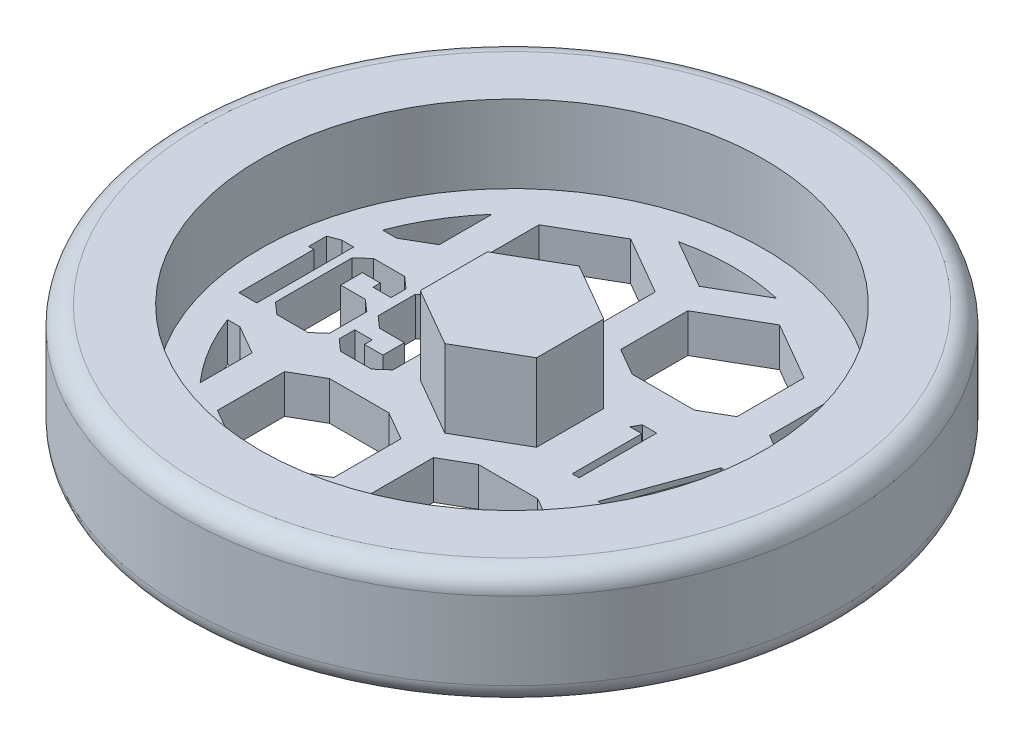
SolidWorks part; units mm, degrees
ref_plane "Front Plane" through (0, 0, 0) normal (0, 0, 1) x (1, 0, 0)
ref_plane "Top Plane" through (0, 0, 0) normal (0, 1, 0) x (1, 0, 0)
ref_plane "Right Plane" through (0, 0, 0) normal (1, 0, 0) x (0, 0, -1)
sketch "Sketch1" plane through (0, 0, 0) normal (0, 0, 1) x (1, 0, 0)
  line L0 (0, 0) -> (25.4, 0)
  line L1 (26.9875, 1.5875) -> (26.9875, 7.9375)
  line L2 (25.4, 9.525) -> (20.6375, 9.525)
  line L3 (20.6375, 9.525) -> (20.6375, 3.175)
  line L4 (20.6375, 3.175) -> (0, 3.175)
  line L5 (0, 3.175) -> (0, 0)
  arc A0 (25.4, 0) -> (26.9875, 1.5875) centre (25.4, 1.5875) ccw
  arc A1 (26.9875, 7.9375) -> (25.4, 9.525) centre (25.4, 7.9375) ccw
  dimension "D5" = 1.5875
  dimension "D1" = 3.175
  dimension "D2" = 6.35
  dimension "D3" = 20.6375
  dimension "D4" = 6.35
revolve "Revolve1" add sketch "Sketch1" angle 360 about L5
sketch "Sketch2" plane through (0, 3.175, 0) normal (0, 1, 0) x (1, 0, 0)
  line L1 (0, 5.4993) -> (-4.7625, 2.7496)
  line L2 (-4.7625, 2.7496) -> (-4.7625, -2.7496)
  line L3 (-4.7625, -2.7496) -> (0, -5.4993)
  line L4 (0, -5.4993) -> (4.7625, -2.7496)
  line L5 (4.7625, -2.7496) -> (4.7625, 2.7496)
  line L6 (4.7625, 2.7496) -> (0, 5.4993)
  circle A0 centre (0, 0) radius 4.7625 construction
  dimension "D1" = 9.525
extrude "Boss-Extrude1" add sketch "Sketch2" along normal blind 6.35
sketch "Sketch3" plane through (0, 3.175, 0) normal (0, 1, 0) x (1, 0, 0)
  line L0 (-4.7625, 0) -> (-20.6375, 0) construction
  line L1 (-4.7625, 2.7496) -> (-4.7625, -2.7496) construction
  line L2 (-4.7625, -3.9688) -> (-20.6375, -3.9688) construction
  line L3 (4.7625, 0) -> (20.6375, 0) construction
  line L4 (4.7625, -2.7496) -> (4.7625, 2.7496) construction
  line L5 (4.7625, -3.175) -> (20.6375, -3.175) construction
  circle A0 centre (0, 0) radius 20.6375 construction
  text T0 "169" font "Jersey M54" height 7.9375
  text T1 "1/4" font "Century Gothic" height 6.35
  dimension "D1" = 3.9688
  dimension "D2" = 3.175
extrude "Cut-Extrude1" cut sketch "Sketch3" against normal through all both and the other way through all
sketch "Sketch4" plane through (0, 3.175, 0) normal (0, 1, 0) x (1, 0, 0)
  line L0 (0, -6.35) -> (0, 6.35)
  line L1 (-16.9469, 6.35) -> (16.9469, 6.35)
  line L2 (-16.9469, -6.35) -> (16.9469, -6.35)
  line L3 (7.4295, -2.7496) -> (12.192, -5.4993)
  line L4 (0, -5.4993) -> (4.7625, -2.7496)
  line L5 (4.7625, -2.7496) -> (4.7625, 2.7496)
  line L6 (4.7625, 2.7496) -> (0, 5.4993)
  line L7 (0, 5.4993) -> (-4.7625, 2.7496)
  line L8 (-4.7625, 2.7496) -> (-4.7625, -2.7496)
  line L9 (-4.7625, -2.7496) -> (0, -5.4993)
  line L10 (6.0325, -15.9479) -> (10.795, -13.1982)
  line L11 (10.795, -13.1982) -> (10.795, -7.699)
  line L12 (10.795, -7.699) -> (6.0325, -4.9493)
  line L13 (6.0325, -4.9493) -> (1.27, -7.699)
  line L14 (1.27, -7.699) -> (1.27, -13.1982)
  line L15 (1.27, -13.1982) -> (6.0325, -15.9479)
  line L16 (7.4295, 2.7496) -> (7.4295, -2.7496)
  line L17 (12.192, 5.4993) -> (7.4295, 2.7496)
  line L18 (16.9545, 2.7496) -> (12.192, 5.4993)
  line L19 (16.9545, -2.7496) -> (16.9545, 2.7496)
  line L20 (12.192, -5.4993) -> (16.9545, -2.7496)
  line L21 (18.2245, -15.9479) -> (22.987, -13.1982)
  line L22 (22.987, -13.1982) -> (22.987, -7.699)
  line L23 (22.987, -7.699) -> (18.2245, -4.9493)
  line L24 (18.2245, -4.9493) -> (13.462, -7.699)
  line L25 (13.462, -7.699) -> (13.462, -13.1982)
  line L26 (13.462, -13.1982) -> (18.2245, -15.9479)
  line L27 (-16.9545, -2.7496) -> (-12.192, -5.4993)
  line L28 (-16.9545, 2.7496) -> (-16.9545, -2.7496)
  line L29 (-12.192, 5.4993) -> (-16.9545, 2.7496)
  line L30 (-7.4295, 2.7496) -> (-12.192, 5.4993)
  line L31 (-7.4295, -2.7496) -> (-7.4295, 2.7496)
  line L32 (-12.192, -5.4993) -> (-7.4295, -2.7496)
  line L33 (-6.1595, -15.9479) -> (-1.397, -13.1982)
  line L34 (-1.397, -13.1982) -> (-1.397, -7.699)
  line L35 (-1.397, -7.699) -> (-6.1595, -4.9493)
  line L36 (-6.1595, -4.9493) -> (-10.922, -7.699)
  line L37 (-10.922, -7.699) -> (-10.922, -13.1982)
  line L38 (-10.922, -13.1982) -> (-6.1595, -15.9479)
  line L39 (-29.1465, -2.7496) -> (-24.384, -5.4993)
  line L40 (-29.1465, 2.7496) -> (-29.1465, -2.7496)
  line L41 (-24.384, 5.4993) -> (-29.1465, 2.7496)
  line L42 (-19.6215, 2.7496) -> (-24.384, 5.4993)
  line L43 (-19.6215, -2.7496) -> (-19.6215, 2.7496)
  line L44 (-24.384, -5.4993) -> (-19.6215, -2.7496)
  line L45 (-18.3515, -15.9479) -> (-13.589, -13.1982)
  line L46 (-13.589, -13.1982) -> (-13.589, -7.699)
  line L47 (-13.589, -7.699) -> (-18.3515, -4.9493)
  line L48 (-18.3515, -4.9493) -> (-23.114, -7.699)
  line L49 (-23.114, -7.699) -> (-23.114, -13.1982)
  line L50 (-23.114, -13.1982) -> (-18.3515, -15.9479)
  line L51 (-4.7625, 18.0784) -> (0, 15.3287)
  line L52 (-4.7625, 23.5776) -> (-4.7625, 18.0784)
  line L53 (0, 26.3273) -> (-4.7625, 23.5776)
  line L54 (4.7625, 23.5776) -> (0, 26.3273)
  line L55 (4.7625, 18.0784) -> (4.7625, 23.5776)
  line L56 (0, 15.3287) -> (4.7625, 18.0784)
  line L57 (6.0325, 4.8801) -> (10.795, 7.6298)
  line L58 (10.795, 7.6298) -> (10.795, 13.129)
  line L59 (10.795, 13.129) -> (6.0325, 15.8787)
  line L60 (6.0325, 15.8787) -> (1.27, 13.129)
  line L61 (1.27, 13.129) -> (1.27, 7.6298)
  line L62 (1.27, 7.6298) -> (6.0325, 4.8801)
  line L63 (-16.9545, 18.0784) -> (-12.192, 15.3287)
  line L64 (-12.192, 15.3287) -> (-7.4295, 18.0784)
  line L65 (-7.4295, 18.0784) -> (-7.4295, 23.5776)
  line L66 (-7.4295, 23.5776) -> (-12.192, 26.3273)
  line L67 (-12.192, 26.3273) -> (-16.9545, 23.5776)
  line L68 (-16.9545, 23.5776) -> (-16.9545, 18.0784)
  line L69 (-29.1465, 18.0784) -> (-24.384, 15.3287)
  line L70 (-24.384, 15.3287) -> (-19.6215, 18.0784)
  line L71 (-19.6215, 18.0784) -> (-19.6215, 23.5776)
  line L72 (-19.6215, 23.5776) -> (-24.384, 26.3273)
  line L73 (-24.384, 26.3273) -> (-29.1465, 23.5776)
  line L74 (-29.1465, 23.5776) -> (-29.1465, 18.0784)
  line L75 (-18.3515, 4.8801) -> (-13.589, 7.6298)
  line L76 (-13.589, 7.6298) -> (-13.589, 13.129)
  line L77 (-13.589, 13.129) -> (-18.3515, 15.8787)
  line L78 (-18.3515, 15.8787) -> (-23.114, 13.129)
  line L79 (-23.114, 13.129) -> (-23.114, 7.6298)
  line L80 (-23.114, 7.6298) -> (-18.3515, 4.8801)
  line L81 (18.2245, 4.8801) -> (22.987, 7.6298)
  line L82 (22.987, 7.6298) -> (22.987, 13.129)
  line L83 (22.987, 13.129) -> (18.2245, 15.8787)
  line L84 (18.2245, 15.8787) -> (13.462, 13.129)
  line L85 (13.462, 13.129) -> (13.462, 7.6298)
  line L86 (13.462, 7.6298) -> (18.2245, 4.8801)
  line L87 (7.4295, 18.0784) -> (12.192, 15.3287)
  line L88 (12.192, 15.3287) -> (16.9545, 18.0784)
  line L89 (16.9545, 18.0784) -> (16.9545, 23.5776)
  line L90 (16.9545, 23.5776) -> (12.192, 26.3273)
  line L91 (12.192, 26.3273) -> (7.4295, 23.5776)
  line L92 (7.4295, 23.5776) -> (7.4295, 18.0784)
  line L93 (-6.1595, 4.8801) -> (-1.397, 7.6298)
  line L94 (-1.397, 7.6298) -> (-1.397, 13.129)
  line L95 (-1.397, 13.129) -> (-6.1595, 15.8787)
  line L96 (-6.1595, 15.8787) -> (-10.922, 13.129)
  line L97 (-10.922, 13.129) -> (-10.922, 7.6298)
  line L98 (-10.922, 7.6298) -> (-6.1595, 4.8801)
  line L99 (-4.7625, -23.5776) -> (0, -26.3273)
  line L100 (-4.7625, -18.0784) -> (-4.7625, -23.5776)
  line L101 (0, -15.3287) -> (-4.7625, -18.0784)
  line L102 (4.7625, -18.0784) -> (0, -15.3287)
  line L103 (4.7625, -23.5776) -> (4.7625, -18.0784)
  line L104 (0, -26.3273) -> (4.7625, -23.5776)
  line L105 (6.0325, -36.7759) -> (10.795, -34.0262)
  line L106 (10.795, -34.0262) -> (10.795, -28.527)
  line L107 (10.795, -28.527) -> (6.0325, -25.7773)
  line L108 (6.0325, -25.7773) -> (1.27, -28.527)
  line L109 (1.27, -28.527) -> (1.27, -34.0262)
  line L110 (1.27, -34.0262) -> (6.0325, -36.7759)
  line L111 (-16.9545, -23.5776) -> (-12.192, -26.3273)
  line L112 (-12.192, -26.3273) -> (-7.4295, -23.5776)
  line L113 (-7.4295, -23.5776) -> (-7.4295, -18.0784)
  line L114 (-7.4295, -18.0784) -> (-12.192, -15.3287)
  line L115 (-12.192, -15.3287) -> (-16.9545, -18.0784)
  line L116 (-16.9545, -18.0784) -> (-16.9545, -23.5776)
  line L117 (-29.1465, -23.5776) -> (-24.384, -26.3273)
  line L118 (-24.384, -26.3273) -> (-19.6215, -23.5776)
  line L119 (-19.6215, -23.5776) -> (-19.6215, -18.0784)
  line L120 (-19.6215, -18.0784) -> (-24.384, -15.3287)
  line L121 (-24.384, -15.3287) -> (-29.1465, -18.0784)
  line L122 (-29.1465, -18.0784) -> (-29.1465, -23.5776)
  line L123 (-18.3515, -36.7759) -> (-13.589, -34.0262)
  line L124 (-13.589, -34.0262) -> (-13.589, -28.527)
  line L125 (-13.589, -28.527) -> (-18.3515, -25.7773)
  line L126 (-18.3515, -25.7773) -> (-23.114, -28.527)
  line L127 (-23.114, -28.527) -> (-23.114, -34.0262)
  line L128 (-23.114, -34.0262) -> (-18.3515, -36.7759)
  line L129 (18.2245, -36.7759) -> (22.987, -34.0262)
  line L130 (22.987, -34.0262) -> (22.987, -28.527)
  line L131 (22.987, -28.527) -> (18.2245, -25.7773)
  line L132 (18.2245, -25.7773) -> (13.462, -28.527)
  line L133 (13.462, -28.527) -> (13.462, -34.0262)
  line L134 (13.462, -34.0262) -> (18.2245, -36.7759)
  line L135 (7.4295, -23.5776) -> (12.192, -26.3273)
  line L136 (12.192, -26.3273) -> (16.9545, -23.5776)
  line L137 (16.9545, -23.5776) -> (16.9545, -18.0784)
  line L138 (16.9545, -18.0784) -> (12.192, -15.3287)
  line L139 (12.192, -15.3287) -> (7.4295, -18.0784)
  line L140 (7.4295, -18.0784) -> (7.4295, -23.5776)
  line L141 (-6.1595, -36.7759) -> (-1.397, -34.0262)
  line L142 (-1.397, -34.0262) -> (-1.397, -28.527)
  line L143 (-1.397, -28.527) -> (-6.1595, -25.7773)
  line L144 (-6.1595, -25.7773) -> (-10.922, -28.527)
  line L145 (-10.922, -28.527) -> (-10.922, -34.0262)
  line L146 (-10.922, -34.0262) -> (-6.1595, -36.7759)
  circle A0 centre (0, 0) radius 18.0975
  circle A1 centre (0, 0) radius 4.7625 construction
  circle A2 centre (6.0325, -10.4486) radius 4.7625 construction
  point P6 (0, 0)
  point P9 (0, 6.35)
  point P12 (0, -6.35)
  dimension "D1" = 36.195
  dimension "D2" = 12.7
  dimension "D3" = 9.525
  dimension "D4" = 2.54
  dimension "D5" = 9.525
  dimension "D6" = 1.27
  dimension "D7" = 2
  dimension "D8" = 3
  dimension "D9" = 2
  dimension "D10" = 2
extrude "Cut-Extrude2" cut sketch "Sketch4" against normal through all both and the other way through all contours L76 A0 L1 L75 | L97 L98 L1 L93 L94 L95 L96 | L56 A0 L51 | L61 L62 L1 L57 L58 L59 L60 | L1 A0 L85 L86 | L14 L15 L10 L11 L12 L2 L13 | L25 A0 L2 L24 | L101 A0 L102 | L37 L38 L33 L34 L35 L2 L36 | L2 A0 L46 L47
